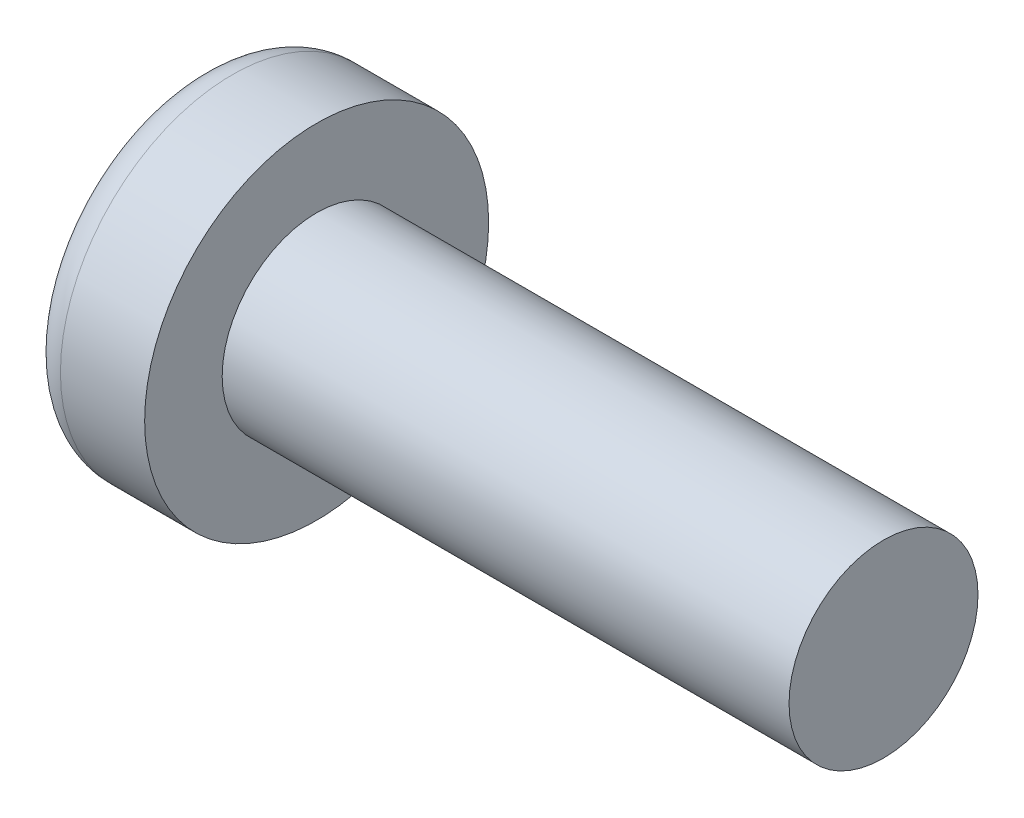
SolidWorks part; units mm, degrees
ref_plane "Plane1" through (0, 0, 0) normal (0, 0, 1) x (1, 0, 0)
ref_plane "Plane2" through (0, 0, 0) normal (0, 1, 0) x (1, 0, 0)
ref_plane "Plane3" through (0, 0, 0) normal (1, 0, 0) x (0, 0, -1)
sketch "BodySke" plane through (0, 0, 0) normal (0, 0, 1) x (1, 0, 0)
  line L0 (1.45, 0.975) -> (1.45, 1.775)
  line L1 (1.95, 6.35) -> (1.95, -3.175) construction
  line L2 (-25.4, 0) -> (127, 0) construction
  line L3 (7.3, 0) -> (0, 0)
  line L4 (1.45, 0.975) -> (7.3, 0.975)
  line L5 (7.3, 0.975) -> (7.3, 0)
  line L6 (0.581, 1.775) -> (1.45, 1.775)
  line L7 (1.45, -0.975) -> (7.3, -0.975) construction
  line L8 (1.45, 6.35) -> (1.45, -3.175) construction
  arc A0 (0.2382, 1.5248) -> (0, 0) centre (5, 0) ccw
  arc A2 (0.2382, 1.5248) -> (0.581, 1.775) centre (0.581, 1.415) cw
  dimension "Head_crown_rad" = 5
  dimension "Head_fillet_rad" = 0.36
  dimension "Diameter" = 1.95
  dimension "Length" = 5.85
  dimension "Head_ht" = 1.45
  dimension "Head_dia" = 3.55
  dimension "Advance" = 0.5
  dimension "Thread_nom" = 5.85
revolve "Base-Revolve" add sketch "BodySke" angle 360 about L2
cosmetic thread "ThreadCosmetic" [suppressed] parameters "Thread_length"=5.35, "Thread_minor"=2.439
sketch "Sketch3" plane through (0, 0, 0) normal (1, 0, 0) x (0, 0, -1)
  line L0 (0.37, -1.45) -> (-0.37, -1.45)
  line L1 (0.37, -1.45) -> (0.37, 1.45)
  line L2 (-0.37, 1.45) -> (0.37, 1.45)
  line L3 (-0.37, 1.45) -> (-0.37, -1.45)
  dimension "Cross_dia" = 2.9
  dimension "D1" = 1.45
  dimension "Cross_width" = 0.74
  dimension "D2" = 0.37
ref_plane "Plane4" through (1.76, 0, 0) normal (1, 0, 0) x (0, 0, -1)
sketch "Sketch4" plane through (1.76, 0, 0) normal (1, 0, 0) x (0, 0, -1)
  line L0 (0.185, -0.185) -> (-0.185, -0.185)
  line L1 (0.185, -0.185) -> (0.185, 0.185)
  line L2 (-0.185, 0.185) -> (0.185, 0.185)
  line L3 (-0.185, 0.185) -> (-0.185, -0.185)
  dimension "D2" = 0.37
  dimension "D1" = 0.37
  dimension "D3" = 0.185
  dimension "D4" = 0.185
loft "Cut-Loft1" cut profiles "Sketch3", "Sketch4"
pattern_circular "CirPattern1" count 2 every 90 about axis through (0, 0, 0) along (1, 0, 0) of "Cut-Loft1"
sketch "ThdSchSke" plane through (0, 0, 0) normal (0, 0, 1) x (1, 0, 0)
  line L0 (1.95, -1.2195) -> (2.1212, -0.975)
  line L1 (1.95, -1.2195) -> (1.7788, -0.975)
  line L2 (1.7788, -0.975) -> (1.7788, -1.2188)
  line L3 (-3.175, 0) -> (5.1513, 0) construction
  line L5 (1.7788, -1.2188) -> (2.1212, -1.2188)
  line L6 (2.1212, -1.2188) -> (2.1212, -0.975)
  dimension "Diameter" = 1.95
  dimension "SideAngle" = 55
  dimension "VeeAngle" = 70
  dimension "Thread_minor" = 2.439
  dimension "Overcut" = 2.4375
  dimension "Start" = 1.95
revolve "ThreadSchematic" [suppressed] cut sketch "ThdSchSke" angle 360 about L3
pattern_linear "ThdSchPat" [suppressed]
equation "\"D1@Sketch3\" = \"Cross_dia@Sketch3\" / 2"
equation "\"D2@Sketch3\" = \"Cross_width@Sketch3\" / 2"
equation "\"D1@Sketch4\" = \"Cross_width@Sketch3\" *.5"
equation "\"D2@Sketch4\" = \"D1@Sketch4\""
equation "\"D3@Sketch4\" = \"D1@Sketch4\" / 2"
equation "\"D4@Sketch4\" = \"D2@Sketch4\" / 2"
equation "\"Thread_length@ThreadCosmetic\" = ((sgn( (\"Length@BodySke\" - \"Advance@BodySke\" ) - \"Thread_nom@BodySke\" )-1)*( (\"Length@BodySke\" - \"Advance@BodySke\" ) - \"Thread_nom@BodySke\" ))/-2+ \"Thread_nom@BodySke\""
equation "\"Thread_minor@ThdSchSke\" = \"Thread_minor@ThreadCosmetic\""
equation "\"Diameter@ThdSchSke\" = \"Diameter@BodySke\""
equation "\"Overcut@ThdSchSke\" = \"Diameter@BodySke\" * 1.25"
equation "\"Start@ThdSchSke\" = \"Head_ht@BodySke\" + \"Length@BodySke\" - \"Thread_length@ThreadCosmetic\"  '---Non-countersunk---"
equation "\"Num_threads@ThdSchPat\" = int( \"Thread_length@ThreadCosmetic\" / \"Advance@BodySke\" + 0.999 )  + 1"
equation "\"Advance@ThdSchPat\" = \"Thread_length@ThreadCosmetic\" /  (\"Num_threads@ThdSchPat\" - 1) 'relax it"
